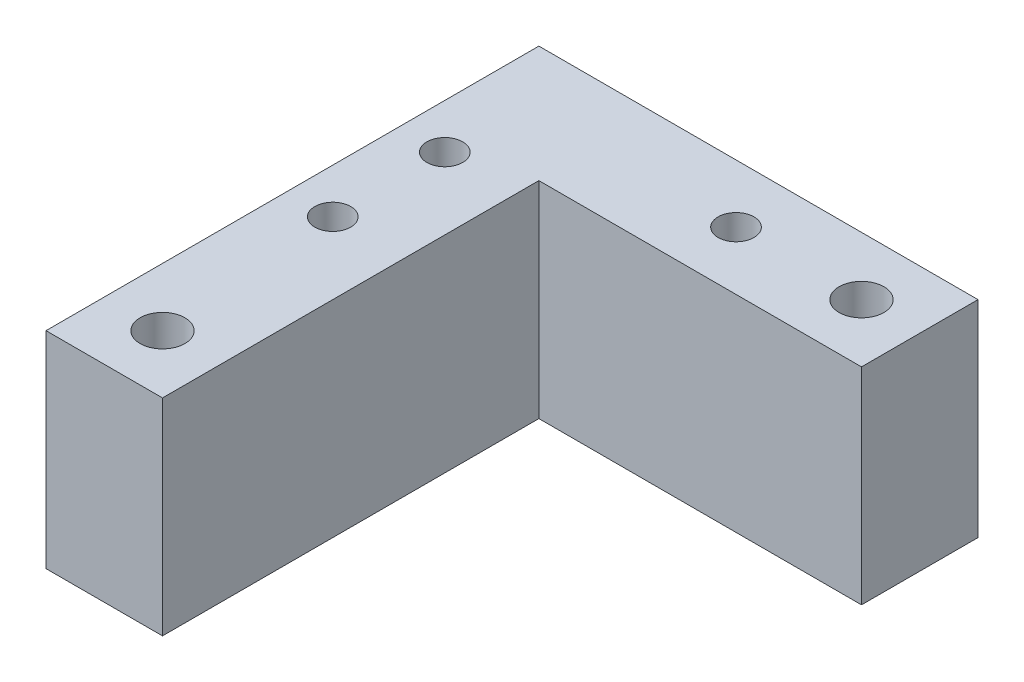
SolidWorks part; units mm, degrees
ref_plane "Front Plane" through (0, 0, 0) normal (0, 0, 1) x (1, 0, 0)
ref_plane "Top Plane" through (0, 0, 0) normal (0, 1, 0) x (1, 0, 0)
ref_plane "Right Plane" through (0, 0, 0) normal (1, 0, 0) x (0, 0, -1)
sketch "Sketch1" plane through (0, 0, 0) normal (0, 1, 0) x (1, 0, 0)
  line L0 (-23.6079, -18.0485) -> (-23.6079, 21.9515)
  line L1 (-23.6079, 21.9515) -> (10.3921, 21.9515)
  line L2 (10.3921, 21.9515) -> (10.3921, 8.9515)
  line L3 (10.3921, 8.9515) -> (-10.6079, 8.9515)
  line L4 (-10.6079, 8.9515) -> (-10.6079, -18.0485)
  line L5 (-10.6079, -18.0485) -> (-23.6079, -18.0485)
  circle A0 centre (-18.6079, -6.0485) radius 2
  circle A1 centre (-18.6079, 6.4515) radius 2
  circle A2 centre (4.8921, 15.4515) radius 2
  point P14 (10.3921, 14.9205)
  dimension "D5" = 4
  dimension "D9" = 4
  dimension "D11" = 4
  dimension "D1" = 34
  dimension "D2" = 40
  dimension "D3" = 13
  dimension "D4" = 13
  dimension "D6" = 12
  dimension "D7" = 5
  dimension "D8" = 12.5
  dimension "D10" = 5
  dimension "D12" = 6.5
  dimension "D13" = 5.5
extrude "Boss-Extrude1" add sketch "Sketch1" along normal blind 23
sketch "Sketch2" plane through (0, 23, 0) normal (0, 1, 0) x (1, 0, 0)
  line L1 (10.3921, 21.9515) -> (25.3921, 21.9515)
  line L2 (10.3921, 21.9515) -> (10.3921, 8.9515)
  line L3 (10.3921, 8.9515) -> (25.3921, 8.9515)
  line L4 (25.3921, 21.9515) -> (25.3921, 8.9515)
  line L5 (-23.6079, -18.0485) -> (-10.6079, -18.0485)
  line L6 (-23.6079, -18.0485) -> (-23.6079, -33.0485)
  line L7 (-23.6079, -33.0485) -> (-10.6079, -33.0485)
  line L8 (-10.6079, -18.0485) -> (-10.6079, -33.0485)
  dimension "D1" = 15
  dimension "D2" = 13
  dimension "D3" = 15
  dimension "D4" = 13
extrude "Boss-Extrude2" add sketch "Sketch2" against normal blind 23
sketch "Sketch3" plane through (0, 23, 0) normal (0, 1, 0) x (1, 0, 0)
  line L0 (-23.6079, 21.9515) -> (-23.6079, -33.0485) construction
  line L1 (-23.6079, -33.0485) -> (-10.6079, -33.0485) construction
  line L2 (-10.6079, 8.9515) -> (25.3921, 8.9515) construction
  line L3 (25.3921, 8.9515) -> (25.3921, 21.9515) construction
  circle A0 centre (18.8921, 15.4515) radius 2.5
  circle A1 centre (-17.1079, -26.5485) radius 2.5
  point P8 (-17.1079, -33.0485)
  dimension "D1" = 5
  dimension "D6" = 5
  dimension "D2" = 6.5
  dimension "D3" = 6.5
  dimension "D4" = 6.5
  dimension "D5" = 6.5
extrude "Cut-Extrude1" cut sketch "Sketch3" against normal blind 23
sketch "Sketch4" plane through (0, 0, 0) normal (0, -1, 0) x (1, 0, 0)
  circle A0 centre (-18.6079, 6.0485) radius 4
  circle A1 centre (-18.6079, -6.4515) radius 4
  circle A2 centre (4.8921, -15.4515) radius 4
  dimension "D1" = 8
  dimension "D2" = 8
  dimension "D3" = 8
extrude "Cut-Extrude2" cut sketch "Sketch4" against normal blind 4.4
